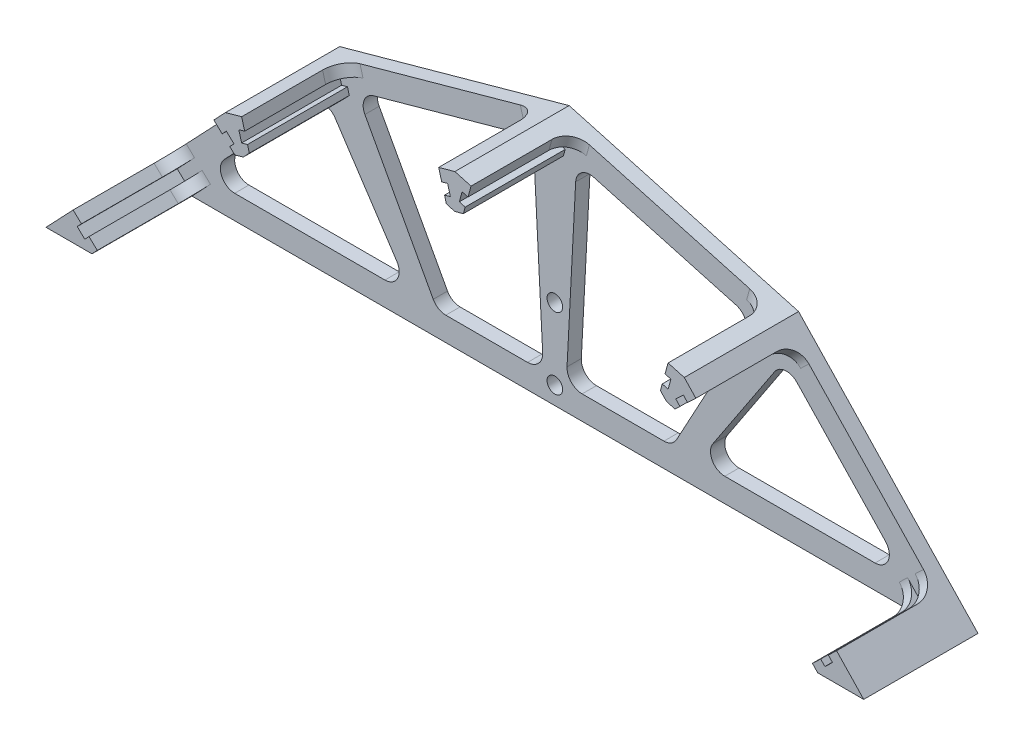
SolidWorks part; units mm, degrees
ref_plane "Front Plane" through (0, 0, 0) normal (0, 0, 1) x (1, 0, 0)
ref_plane "Top Plane" through (0, 0, 0) normal (0, 1, 0) x (1, 0, 0)
ref_plane "Right Plane" through (0, 0, 0) normal (1, 0, 0) x (0, 0, -1)
sketch "Sketch1" plane through (0, 0, 0) normal (0, 0, 1) x (1, 0, 0)
  line L0 (0, -46.7747) -> (0, 46.7747) construction
  line L2 (82.5993, -2.8559) -> (0, -46.7747) construction
  line L3 (0, 46.7747) -> (48.1815, 33.4128)
  line L4 (48.1815, 33.4128) -> (0, -46.7747) construction
  line L5 (48.1815, 33.4128) -> (82.5993, -2.8559)
  line L7 (-48.1815, 33.4128) -> (-82.5993, -2.8559)
  line L8 (-48.1815, 33.4128) -> (0, -46.7747) construction
  line L9 (0, 46.7747) -> (-48.1815, 33.4128)
  line L10 (-82.5993, -2.8559) -> (0, -46.7747) construction
  line L11 (-78.9724, -6.2977) -> (78.9724, -6.2977)
  line L12 (-78.9724, -6.2977) -> (-85.8654, -6.2977)
  line L13 (-85.8654, -6.2977) -> (-82.5993, -2.8559)
  line L14 (78.9724, -6.2977) -> (85.8654, -6.2977)
  line L15 (85.8654, -6.2977) -> (82.5993, -2.8559)
  dimension "D2" = 31
  dimension "D3" = 31
  dimension "D4" = 50
  dimension "D1" = 5
extrude "Boss-Extrude1" add sketch "Sketch1" along normal blind 3
sketch "Sketch2" plane through (0, 0, 3) normal (0, 0, 1) x (1, 0, 0)
  line L0 (-48.1815, 33.4128) -> (-44.7799, 34.3562)
  line L1 (0, 46.7747) -> (-48.1815, 33.4128) construction
  line L2 (-44.7799, 34.3562) -> (-44.1385, 32.0434)
  line L3 (-42.9092, 27.6107) -> (-46.3109, 26.6674)
  line L4 (-46.3109, 26.6674) -> (-48.1815, 33.4128) construction
  line L5 (-5.6614, 41.5726) -> (-1.2328, 42.8007) construction
  line L6 (1.8707, 40.0293) -> (0, 46.7747) construction
  line L7 (-1.5309, 39.086) -> (1.8707, 40.0293)
  line L8 (-2.1723, 41.3987) -> (-1.5309, 39.086)
  line L9 (-24.0908, 40.0938) -> (-22.238, 33.4128) construction
  line L10 (0, 46.7747) -> (-48.1815, 33.4128) construction
  line L11 (-45.372, 31.7014) -> (-44.7841, 29.5814)
  line L12 (-44.1385, 32.0434) -> (-45.372, 31.7014)
  line L13 (-40.6495, 31.8695) -> (-45.078, 30.6414) construction
  line L14 (-43.5506, 29.9235) -> (-44.7841, 29.5814)
  line L15 (-43.5506, 29.9235) -> (-42.9092, 27.6107)
  line L16 (-2.1723, 41.3987) -> (-0.9389, 41.7407)
  line L17 (-2.7602, 43.5187) -> (-1.5268, 43.8607)
  line L18 (-1.5268, 43.8607) -> (-0.9389, 41.7407)
  line L19 (-3.4016, 45.8314) -> (-2.7602, 43.5187)
  line L20 (0, 46.7747) -> (-3.4016, 45.8314)
  line L21 (0, 46.7747) -> (0, -46.7747) construction
  line L22 (40.6495, 31.8695) -> (45.078, 30.6414) construction
  line L23 (24.0908, 40.0938) -> (22.238, 33.4128) construction
  line L24 (1.5309, 39.086) -> (-1.8707, 40.0293)
  line L25 (-1.8707, 40.0293) -> (0, 46.7747) construction
  line L26 (5.6614, 41.5726) -> (1.2328, 42.8007) construction
  line L27 (46.3109, 26.6674) -> (48.1815, 33.4128) construction
  line L28 (42.9092, 27.6107) -> (46.3109, 26.6674)
  line L29 (0, 46.7747) -> (3.4016, 45.8314)
  line L30 (3.4016, 45.8314) -> (2.7602, 43.5187)
  line L31 (1.5268, 43.8607) -> (0.9389, 41.7407)
  line L32 (2.7602, 43.5187) -> (1.5268, 43.8607)
  line L33 (2.1723, 41.3987) -> (0.9389, 41.7407)
  line L34 (43.5506, 29.9235) -> (42.9092, 27.6107)
  line L35 (43.5506, 29.9235) -> (44.7841, 29.5814)
  line L36 (44.1385, 32.0434) -> (45.372, 31.7014)
  line L37 (45.372, 31.7014) -> (44.7841, 29.5814)
  line L38 (2.1723, 41.3987) -> (1.5309, 39.086)
  line L39 (44.7799, 34.3562) -> (44.1385, 32.0434)
  line L40 (48.1815, 33.4128) -> (44.7799, 34.3562)
  line L41 (48.1815, 33.4128) -> (0, -46.7747) construction
  line L42 (0, -46.7747) -> (-48.1815, 33.4128) construction
  line L43 (-75.7652, -4.371) -> (-82.5993, -2.8559) construction
  line L44 (-50.355, 26.0379) -> (-47.1915, 29.3715) construction
  line L45 (-65.3904, 15.2784) -> (-60.3613, 10.506) construction
  line L46 (-75.0917, -5.1138) -> (-77.5216, -7.6744)
  line L47 (-77.5216, -7.6744) -> (-82.5993, -2.8559)
  line L48 (-75.3482, -0.2995) -> (-78.5116, -3.6331) construction
  line L49 (-43.1039, 28.5943) -> (-48.1815, 33.4128) construction
  line L50 (-45.5338, 26.0337) -> (-43.1039, 28.5943)
  line L51 (-82.5993, -2.8559) -> (-80.1694, -0.2953)
  line L52 (-80.1694, -0.2953) -> (-78.4285, -1.9474)
  line L53 (-79.3096, -2.8759) -> (-77.7137, -4.3903)
  line L54 (-78.4285, -1.9474) -> (-79.3096, -2.8759)
  line L55 (-76.8326, -3.4618) -> (-77.7137, -4.3903)
  line L56 (-47.2747, 27.6858) -> (-45.5338, 26.0337)
  line L57 (-47.2747, 27.6858) -> (-46.3936, 28.6143)
  line L58 (-48.8705, 29.2002) -> (-47.9894, 30.1287)
  line L59 (-47.9894, 30.1287) -> (-46.3936, 28.6143)
  line L60 (-76.8326, -3.4618) -> (-75.0917, -5.1138)
  line L61 (-50.6114, 30.8522) -> (-48.8705, 29.2002)
  line L62 (-48.1815, 33.4128) -> (-50.6114, 30.8522)
  line L63 (45.5338, 26.0337) -> (43.1039, 28.5943)
  line L64 (43.1039, 28.5943) -> (48.1815, 33.4128) construction
  line L65 (75.3482, -0.2995) -> (78.5116, -3.6331) construction
  line L66 (77.5216, -7.6744) -> (82.5993, -2.8559)
  line L67 (75.0917, -5.1138) -> (77.5216, -7.6744)
  line L68 (65.3904, 15.2784) -> (60.3613, 10.506) construction
  line L69 (50.355, 26.0379) -> (47.1915, 29.3715) construction
  line L70 (48.1815, 33.4128) -> (50.6114, 30.8522)
  line L71 (50.6114, 30.8522) -> (48.8705, 29.2002)
  line L72 (76.8326, -3.4618) -> (75.0917, -5.1138)
  line L73 (47.9894, 30.1287) -> (46.3936, 28.6143)
  line L74 (48.8705, 29.2002) -> (47.9894, 30.1287)
  line L75 (47.2747, 27.6858) -> (46.3936, 28.6143)
  line L76 (47.2747, 27.6858) -> (45.5338, 26.0337)
  line L77 (76.8326, -3.4618) -> (77.7137, -4.3903)
  line L78 (78.4285, -1.9474) -> (79.3096, -2.8759)
  line L79 (79.3096, -2.8759) -> (77.7137, -4.3903)
  line L80 (80.1694, -0.2953) -> (78.4285, -1.9474)
  line L81 (82.5993, -2.8559) -> (80.1694, -0.2953)
  line L82 (-40.6495, 31.8695) -> (-47.2462, 30.0401) construction
  line L83 (-82.5993, -2.8559) -> (-85.8654, -6.2977)
  line L84 (-85.8654, -6.2977) -> (-78.9724, -6.2977)
  line L85 (-85.8654, -6.2977) -> (85.8654, -6.2977) construction
  line L86 (-78.9724, -6.2977) -> (-82.5993, -2.8559)
  line L87 (77.5216, -7.6744) -> (82.5993, -2.8559)
  line L88 (85.8654, -6.2977) -> (78.9724, -6.2977)
  line L89 (82.5993, -2.8559) -> (85.8654, -6.2977)
  point P20 (-40.7831, 32.3513)
  point P94 (-47.2462, 30.0401)
  dimension "D1" = 7
  dimension "D2" = 22.75
  dimension "D3" = 1.1
  dimension "D4" = 1.28
extrude "Boss-Extrude2" add sketch "Sketch2" along normal blind 21
sketch "Sketch3" plane through (0, 0, 3) normal (0, 0, 1) x (1, 0, 0)
  line L0 (0, -46.7747) -> (-74.2276, -1.2977) construction
  line L1 (-69.421, 3.7674) -> (-50.8282, 23.3601)
  line L2 (-46.1504, 22.9509) -> (-33.1822, 3.3581)
  line L3 (-35.6839, -1.2977) -> (-67.2449, -1.2977)
  line L4 (-25.5437, 0.2708) -> (-39.8978, 26.7078)
  line L5 (-38.063, 31.0302) -> (-8.1664, 39.3213)
  line L6 (-4.3688, 36.5874) -> (-2.5585, 2.0435)
  line L7 (-5.7291, -1.2977) -> (-22.9072, -1.2977)
  line L8 (-48.1815, 33.4128) -> (-82.5993, -2.8559) construction
  line L9 (0, 46.7747) -> (-48.1815, 33.4128) construction
  line L10 (-78.9724, -6.2977) -> (78.9724, -6.2977) construction
  line L11 (-48.1815, 33.4128) -> (0, -46.7747) construction
  line L12 (0, -46.7747) -> (0, 46.7747) construction
  line L13 (-2.5585, 2.0435) -> (0, -46.7747) construction
  line L14 (0, 46.7747) -> (0, 0) construction
  line L15 (5.7291, -1.2977) -> (22.9072, -1.2977)
  line L16 (4.3688, 36.5874) -> (2.5585, 2.0435)
  line L17 (38.063, 31.0302) -> (8.1664, 39.3213)
  line L18 (25.5437, 0.2708) -> (39.8978, 26.7078)
  line L19 (35.6839, -1.2977) -> (67.2449, -1.2977)
  line L20 (46.1504, 22.9509) -> (33.1822, 3.3581)
  line L21 (69.421, 3.7674) -> (50.8282, 23.3601)
  arc A0 (-35.6839, -1.2977) -> (-33.1822, 3.3581) centre (-35.6839, 1.7023) ccw
  arc A1 (-50.8282, 23.3601) -> (-46.1504, 22.9509) centre (-48.652, 21.2951) cw
  arc A2 (-69.421, 3.7674) -> (-67.2449, -1.2977) centre (-67.2449, 1.7023) ccw
  arc A3 (-25.5437, 0.2708) -> (-22.9072, -1.2977) centre (-22.9072, 1.7023) ccw
  arc A4 (-39.8978, 26.7078) -> (-38.063, 31.0302) centre (-37.2613, 28.1393) cw
  arc A5 (-8.1664, 39.3213) -> (-4.3688, 36.5874) centre (-7.3647, 36.4304) cw
  arc A6 (-2.5585, 2.0435) -> (-5.7291, -1.2977) centre (-5.7291, 1.8773) cw
  arc A7 (2.5585, 2.0435) -> (5.7291, -1.2977) centre (5.7291, 1.8773) ccw
  arc A8 (8.1664, 39.3213) -> (4.3688, 36.5874) centre (7.3647, 36.4304) ccw
  arc A9 (39.8978, 26.7078) -> (38.063, 31.0302) centre (37.2613, 28.1393) ccw
  arc A10 (25.5437, 0.2708) -> (22.9072, -1.2977) centre (22.9072, 1.7023) cw
  arc A11 (69.421, 3.7674) -> (67.2449, -1.2977) centre (67.2449, 1.7023) cw
  arc A12 (50.8282, 23.3601) -> (46.1504, 22.9509) centre (48.652, 21.2951) ccw
  arc A13 (35.6839, -1.2977) -> (33.1822, 3.3581) centre (35.6839, 1.7023) cw
  circle A14 centre (0, -2.5545) radius 1.6425
  circle A15 centre (0, 12.4455) radius 1.6425
  dimension "D1" = 5
  dimension "D6" = 3
  dimension "D7" = 3
  dimension "D8" = 3.175
  dimension "D2" = 5
  dimension "D3" = 5
  dimension "D4" = 2.5
  dimension "D5" = 2.5
  dimension "D9" = 3
  dimension "D10" = 15
extrude "Cut-Extrude1" cut sketch "Sketch3" against normal through all
sketch "Sketch5" plane through (0, 0, 24) normal (0, 0, 1) x (1, 0, 0)
  line L0 (-73.6877, -11.8812) -> (-66.4917, 7.1034)
  line L1 (-66.4917, 7.1034) -> (-31.6623, 32.4212)
  line L2 (-31.6623, 32.4212) -> (-32.1393, 38.3933)
  line L3 (97.2019, -18.6925) -> (-73.6877, -11.8812)
  arc A0 (-32.1393, 38.3933) -> (97.2019, -18.6925) centre (47.9525, 44.7906) cw
extrude "Cut-Extrude2" [suppressed] cut sketch "Sketch5" against normal through all
fillet "Fillet3" radius 4 1 edges at (-79.2989, -1.1214, 3)
fillet "Fillet4" radius 4 9 edges at (79.2989, -1.1214, 3) (49.741, 30.0262, 3) (44.4592, 33.1998, 3) (3.0809, 44.675, 3) (-3.0809, 44.675, 3) (-75.9622, -4.2878, 3) (75.9622, -4.2878, 3)
equation "\"D3@Sketch1\"=\"D2@Sketch1\""
equation "\"D5@Sketch3\"=\"D4@Sketch3\""
